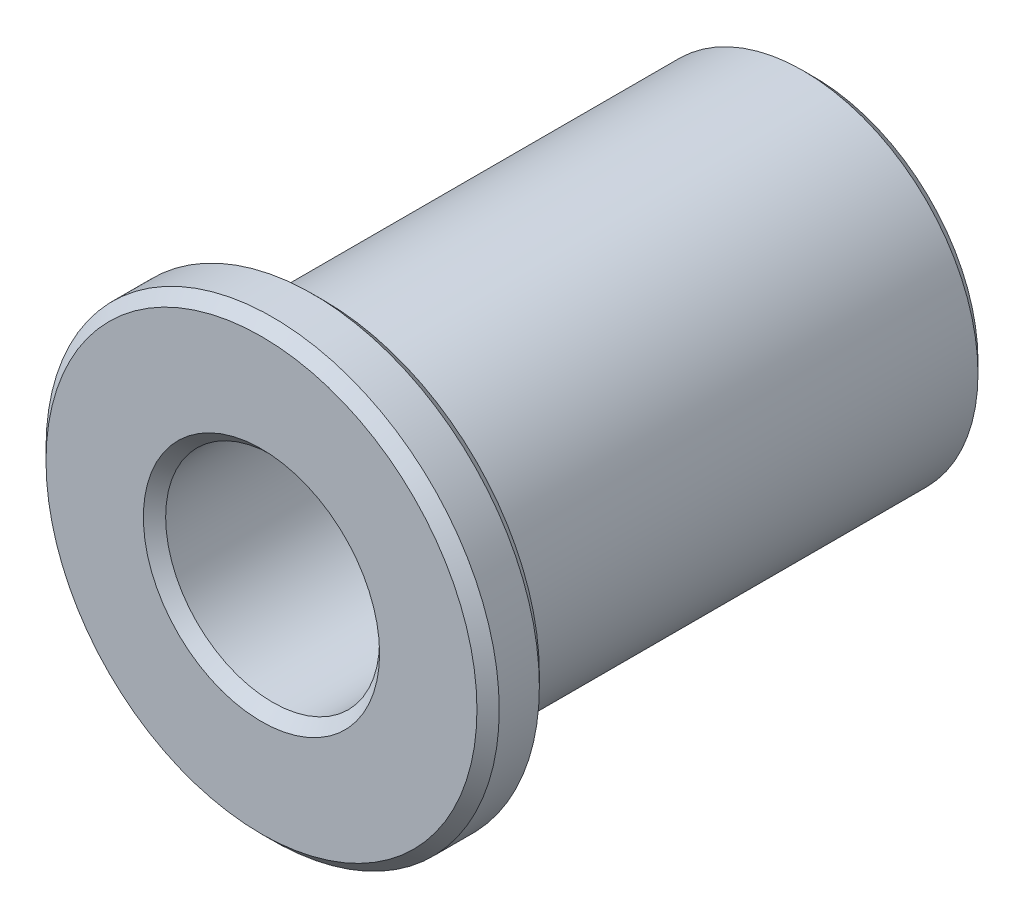
SolidWorks part; units mm, degrees
material "Commercial Bronze, UNS C22000 (90-10 Bronze)"
ref_plane "Front Plane" through (0, 0, 0) normal (0, 0, 1) x (1, 0, 0)
ref_plane "Top Plane" through (0, 0, 0) normal (0, 1, 0) x (1, 0, 0)
ref_plane "Right Plane" through (0, 0, 0) normal (1, 0, 0) x (0, 0, -1)
sketch "Sketch1" plane through (0, 0, 0) normal (0, 0, 1) x (1, 0, 0)
  circle A0 centre (0, 0) radius 3.925
  dimension "D1" = 7.85
extrude "Boss-Extrude1" add sketch "Sketch1" against normal blind 11
sketch "Sketch2" plane through (0, 0, 0) normal (0, 0, 1) x (1, 0, 0)
  circle A0 centre (0, 0) radius 5.0841
extrude "Boss-Extrude2" add sketch "Sketch2" along normal blind 1.4
sketch "Sketch3" plane through (0, 0, 1.4) normal (0, 0, 1) x (1, 0, 0)
  circle A0 centre (0, 0) radius 2.4
  dimension "D1" = 4.8
extrude "Cut-Extrude1" cut sketch "Sketch3" against normal through all
chamfer "Chamfer1" distance 0.25 angle 45 5 edges at (5.0841, 0, 0) (5.0841, 0, 1.4) (3.925, 0, -11) (2.4, 0, -11) (2.4, 0, 1.4)
